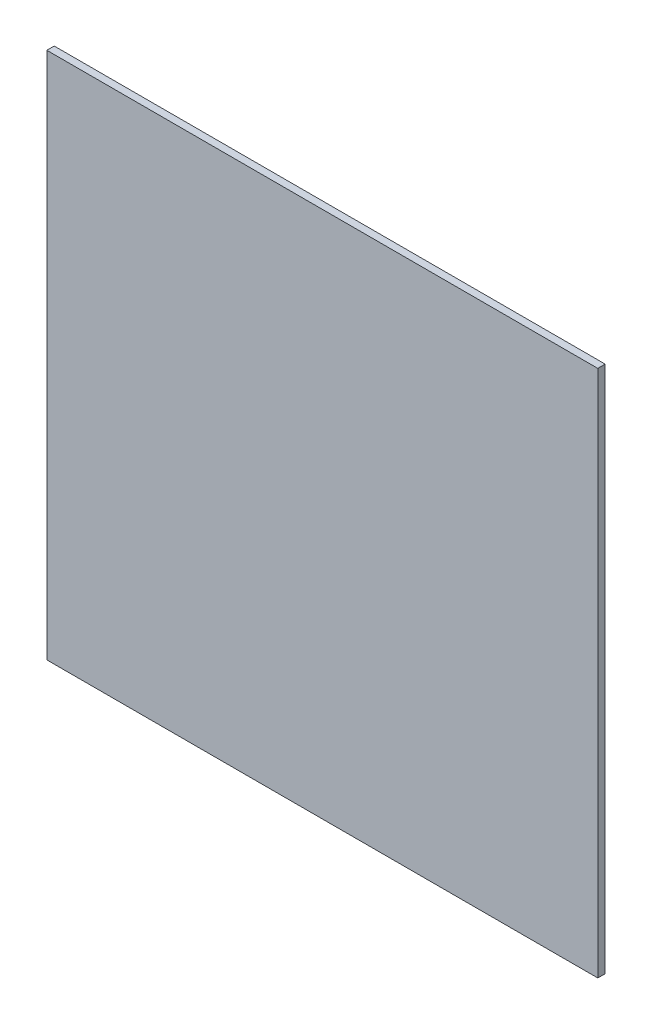
SolidWorks part; units mm, degrees
ref_plane "Front Plane" through (0, 0, 0) normal (0, 0, 1) x (1, 0, 0)
ref_plane "Top Plane" through (0, 0, 0) normal (0, 1, 0) x (1, 0, 0)
ref_plane "Right Plane" through (0, 0, 0) normal (1, 0, 0) x (0, 0, -1)
sketch "Sketch1" plane through (0, 0, 0) normal (0, 0, 1) x (1, 0, 0)
  line L1 (-161.925, -155.1686) -> (161.925, -155.1686)
  line L2 (-161.925, -155.1686) -> (-161.925, 155.1686)
  line L3 (-161.925, 155.1686) -> (161.925, 155.1686)
  line L4 (161.925, -155.1686) -> (161.925, 155.1686)
  line L5 (-161.925, -155.1686) -> (161.925, 155.1686) construction
  line L6 (-161.925, 155.1686) -> (161.925, -155.1686) construction
  point P0 (0, 0)
  dimension "D1" = 323.85
  dimension "D2" = 310.3372
extrude "Boss-Extrude1" add sketch "Sketch1" along normal blind 4.3434
